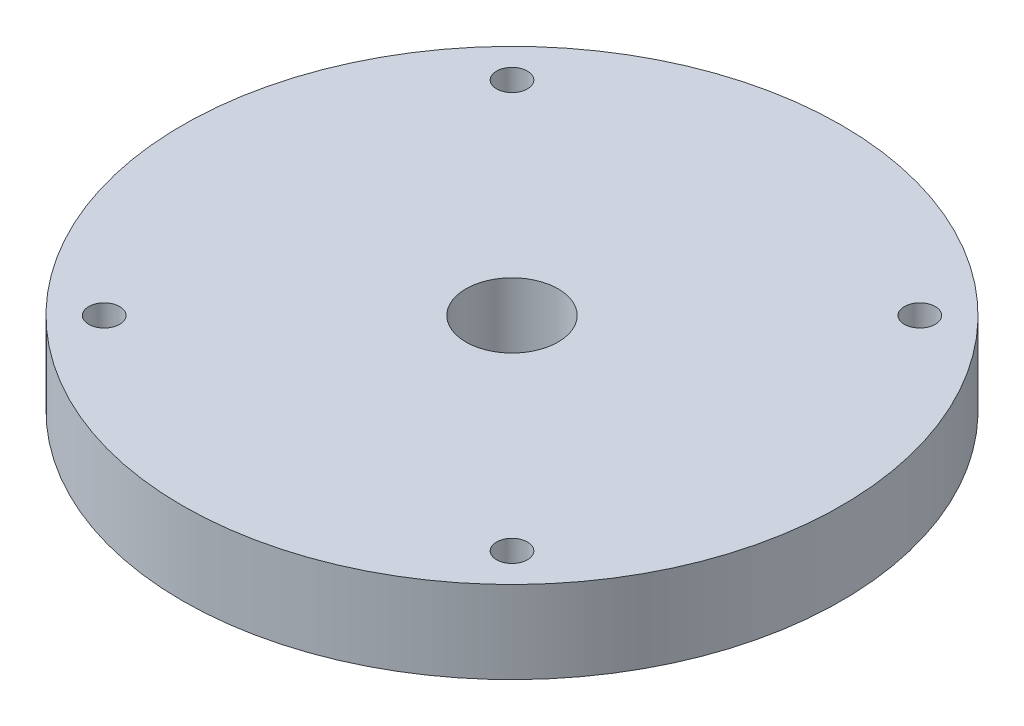
SolidWorks part; units mm, degrees
ref_plane "Front Plane" through (0, 0, 0) normal (0, 0, 1) x (1, 0, 0)
ref_plane "Top Plane" through (0, 0, 0) normal (0, 1, 0) x (1, 0, 0)
ref_plane "Right Plane" through (0, 0, 0) normal (1, 0, 0) x (0, 0, -1)
sketch "Sketch1" plane through (0, 0, 0) normal (0, 1, 0) x (1, 0, 0)
  line L0 (-15.7154, 15.7154) -> (0, 0) construction
  line L1 (0, 0) -> (0, 26) construction
  circle A0 centre (0, 0) radius 25.4
  circle A2 centre (-15.7154, 15.7154) radius 1.1906
  circle A3 centre (15.7154, 15.7154) radius 1.1906
  circle A5 centre (15.7154, -15.7154) radius 1.1906
  circle A7 centre (-15.7154, -15.7154) radius 1.1906
  circle A8 centre (0, 0) radius 17.5 construction
  circle A10 centre (0, 0) radius 3.556
  dimension "D1" = 2.3813
  dimension "D3" = 2.3813
  dimension "D6" = 7.112
  dimension "D7" = 2.3813
  dimension "D8" = 2.3813
  dimension "D9" = 50.8
  dimension "D2" = 45
  dimension "D4" = 22.225
  dimension "D5" = 26
extrude "Boss-Extrude1" add sketch "Sketch1" along normal blind 6.35
